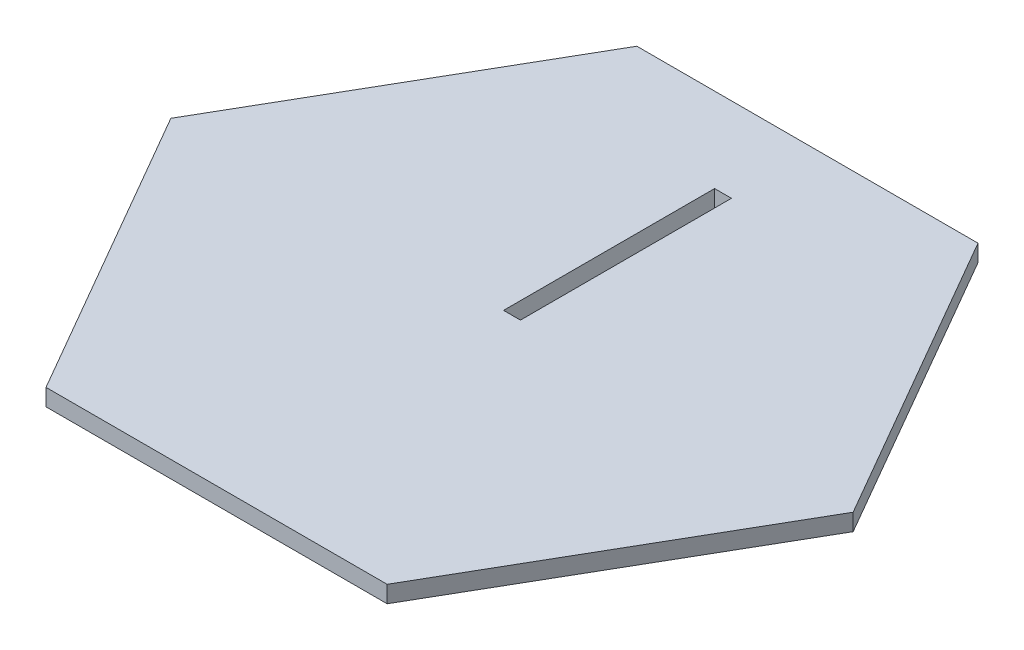
SolidWorks part; units mm, degrees
ref_plane "Front Plane" through (0, 0, 0) normal (0, 0, 1) x (1, 0, 0)
ref_plane "Top Plane" through (0, 0, 0) normal (0, 1, 0) x (1, 0, 0)
ref_plane "Right Plane" through (0, 0, 0) normal (1, 0, 0) x (0, 0, -1)
sketch "Sketch1" plane through (0, 0, 0) normal (0, 1, 0) x (1, 0, 0)
  line L1 (-20.2073, -35) -> (20.2073, -35)
  line L2 (20.2073, -35) -> (40.4145, 0)
  line L3 (40.4145, 0) -> (20.2073, 35)
  line L4 (20.2073, 35) -> (-20.2073, 35)
  line L5 (-20.2073, 35) -> (-40.4145, 0)
  line L6 (-40.4145, 0) -> (-20.2073, -35)
  circle A0 centre (0, 0) radius 35 construction
  dimension "D1" = 70
extrude "Boss-Extrude1" add sketch "Sketch1" along normal blind 2
sketch "Sketch2" plane through (0, 2, 0) normal (0, 1, 0) x (1, 0, 0)
  line L0 (0, 0) -> (0, 25)
  dimension "D1" = 25
extrude "Cut-Extrude-Thin1" cut sketch "Sketch2" against normal through all and the other way through all thin thin type mid plane wall 2
